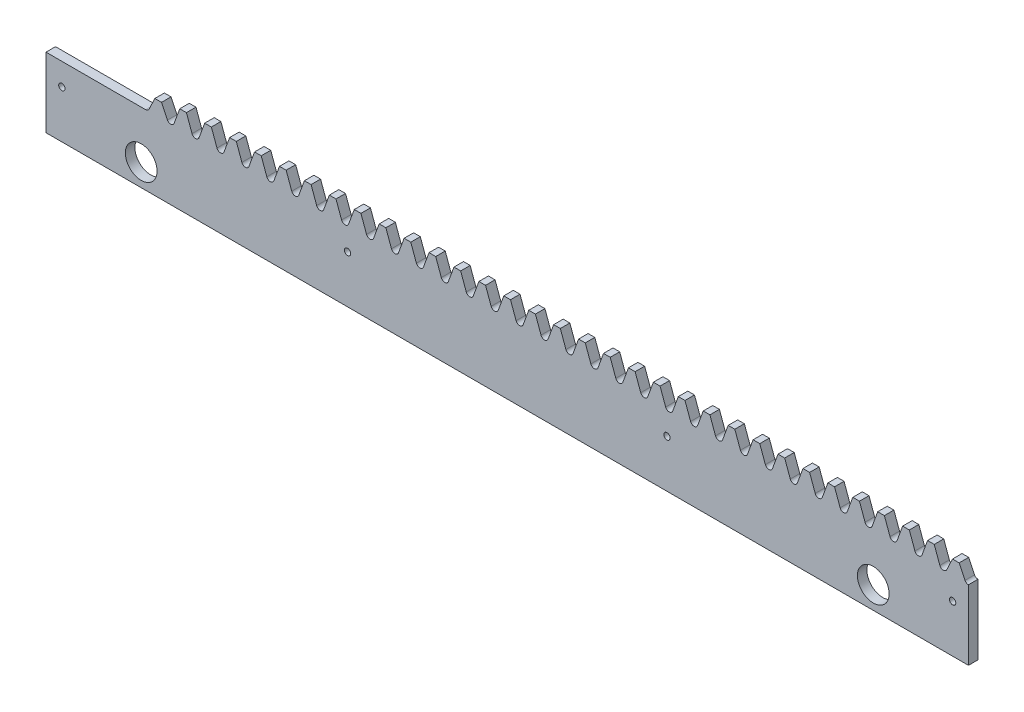
SolidWorks part; units mm, degrees
ref_plane "Plane1" through (0, 0, 0) normal (0, 0, 1) x (1, 0, 0)
ref_plane "Plane2" through (0, 0, 0) normal (0, 1, 0) x (1, 0, 0)
ref_plane "Plane3" through (0, 0, 0) normal (1, 0, 0) x (0, 0, -1)
sketch "Esquisse1" plane through (0, 0, 0) normal (0, 0, 1) x (1, 0, 0)
  line L0 (-11.781, 22) -> (19.635, 22)
  line L1 (23.5619, 29.1362) -> (23.5619, 19.2192) construction
  line L2 (-16.2297, 22) -> (24.6155, 22) construction
  line L3 (18.2522, 26.5) -> (283.3605, 26.5) construction
  line L4 (22.5084, 28.8854) -> (22.5084, 23.1798) construction
  line L5 (22.5084, 26.5) -> (20.6365, 22.5562)
  line L6 (24.6155, 26.5) -> (26.4874, 22.5562)
  line L8 (22.5084, 26.5) -> (24.6155, 26.5)
  line L10 (275.9429, 26.742) -> (275.9429, 19.9201) construction
  line L11 (273.8358, 26.742) -> (273.8358, 19.9201) construction
  line L12 (273.8358, 26.5) -> (272.0069, 22.6314)
  line L13 (275.9429, 26.5) -> (277.7718, 22.6314)
  line L14 (273.8358, 26.5) -> (275.9429, 26.5)
  line L20 (28.5976, 22.7763) -> (30.3624, 27.625)
  line L21 (30.3624, 27.625) -> (32.4695, 27.625)
  line L22 (34.2343, 22.7763) -> (32.4695, 27.625)
  line L23 (36.4515, 22.7763) -> (38.2163, 27.625)
  line L24 (38.2163, 27.625) -> (40.3235, 27.625)
  line L25 (42.0883, 22.7763) -> (40.3235, 27.625)
  line L26 (44.3055, 22.7763) -> (46.0703, 27.625)
  line L27 (46.0703, 27.625) -> (48.1775, 27.625)
  line L28 (49.9423, 22.7763) -> (48.1775, 27.625)
  line L29 (52.1595, 22.7763) -> (53.9243, 27.625)
  line L30 (53.9243, 27.625) -> (56.0314, 27.625)
  line L31 (57.7962, 22.7763) -> (56.0314, 27.625)
  line L32 (60.0135, 22.7763) -> (61.7783, 27.625)
  line L33 (61.7783, 27.625) -> (63.8854, 27.625)
  line L34 (65.6502, 22.7763) -> (63.8854, 27.625)
  line L35 (67.8675, 22.7763) -> (69.6323, 27.625)
  line L36 (69.6323, 27.625) -> (71.7394, 27.625)
  line L37 (73.5042, 22.7763) -> (71.7394, 27.625)
  line L38 (75.7215, 22.7763) -> (77.4862, 27.625)
  line L39 (77.4862, 27.625) -> (79.5934, 27.625)
  line L40 (81.3582, 22.7763) -> (79.5934, 27.625)
  line L41 (83.5754, 22.7763) -> (85.3402, 27.625)
  line L42 (85.3402, 27.625) -> (87.4474, 27.625)
  line L43 (89.2122, 22.7763) -> (87.4474, 27.625)
  line L44 (91.4294, 22.7763) -> (93.1942, 27.625)
  line L45 (93.1942, 27.625) -> (95.3013, 27.625)
  line L46 (97.0661, 22.7763) -> (95.3013, 27.625)
  line L47 (99.2834, 22.7763) -> (101.0482, 27.625)
  line L48 (101.0482, 27.625) -> (103.1553, 27.625)
  line L49 (104.9201, 22.7763) -> (103.1553, 27.625)
  line L50 (107.1374, 22.7763) -> (108.9022, 27.625)
  line L51 (108.9022, 27.625) -> (111.0093, 27.625)
  line L52 (112.7741, 22.7763) -> (111.0093, 27.625)
  line L53 (114.9914, 22.7763) -> (116.7562, 27.625)
  line L54 (116.7562, 27.625) -> (118.8633, 27.625)
  line L55 (120.6281, 22.7763) -> (118.8633, 27.625)
  line L56 (122.8453, 22.7763) -> (124.6101, 27.625)
  line L57 (124.6101, 27.625) -> (126.7173, 27.625)
  line L58 (128.4821, 22.7763) -> (126.7173, 27.625)
  line L59 (130.6993, 22.7763) -> (132.4641, 27.625)
  line L60 (132.4641, 27.625) -> (134.5713, 27.625)
  line L61 (136.3361, 22.7763) -> (134.5713, 27.625)
  line L62 (138.5533, 22.7763) -> (140.3181, 27.625)
  line L63 (140.3181, 27.625) -> (142.4252, 27.625)
  line L64 (144.19, 22.7763) -> (142.4252, 27.625)
  line L65 (146.4073, 22.7763) -> (148.1721, 27.625)
  line L66 (148.1721, 27.625) -> (150.2792, 27.625)
  line L67 (152.044, 22.7763) -> (150.2792, 27.625)
  line L68 (154.2613, 22.7763) -> (156.0261, 27.625)
  line L69 (156.0261, 27.625) -> (158.1332, 27.625)
  line L70 (159.898, 22.7763) -> (158.1332, 27.625)
  line L71 (162.1153, 22.7763) -> (163.88, 27.625)
  line L72 (163.88, 27.625) -> (165.9872, 27.625)
  line L73 (167.752, 22.7763) -> (165.9872, 27.625)
  line L74 (169.9692, 22.7763) -> (171.734, 27.625)
  line L75 (171.734, 27.625) -> (173.8412, 27.625)
  line L76 (175.606, 22.7763) -> (173.8412, 27.625)
  line L77 (177.8232, 22.7763) -> (179.588, 27.625)
  line L78 (179.588, 27.625) -> (181.6951, 27.625)
  line L79 (183.4599, 22.7763) -> (181.6951, 27.625)
  line L80 (185.6772, 22.7763) -> (187.442, 27.625)
  line L81 (187.442, 27.625) -> (189.5491, 27.625)
  line L82 (191.3139, 22.7763) -> (189.5491, 27.625)
  line L83 (193.5312, 22.7763) -> (195.296, 27.625)
  line L84 (195.296, 27.625) -> (197.4031, 27.625)
  line L85 (199.1679, 22.7763) -> (197.4031, 27.625)
  line L86 (201.3852, 22.7763) -> (203.15, 27.625)
  line L87 (203.15, 27.625) -> (205.2571, 27.625)
  line L88 (207.0219, 22.7763) -> (205.2571, 27.625)
  line L89 (209.2391, 22.7763) -> (211.0039, 27.625)
  line L90 (211.0039, 27.625) -> (213.1111, 27.625)
  line L91 (214.8759, 22.7763) -> (213.1111, 27.625)
  line L92 (217.0931, 22.7763) -> (218.8579, 27.625)
  line L93 (218.8579, 27.625) -> (220.9651, 27.625)
  line L94 (222.7298, 22.7763) -> (220.9651, 27.625)
  line L95 (224.9471, 22.7763) -> (226.7119, 27.625)
  line L96 (226.7119, 27.625) -> (228.819, 27.625)
  line L97 (230.5838, 22.7763) -> (228.819, 27.625)
  line L98 (232.8011, 22.7763) -> (234.5659, 27.625)
  line L99 (234.5659, 27.625) -> (236.673, 27.625)
  line L100 (238.4378, 22.7763) -> (236.673, 27.625)
  line L101 (240.6551, 22.7763) -> (242.4199, 27.625)
  line L102 (242.4199, 27.625) -> (244.527, 27.625)
  line L103 (246.2918, 22.7763) -> (244.527, 27.625)
  line L104 (248.509, 22.7763) -> (250.2738, 27.625)
  line L105 (250.2738, 27.625) -> (252.381, 27.625)
  line L106 (254.1458, 22.7763) -> (252.381, 27.625)
  line L107 (256.363, 22.7763) -> (258.1278, 27.625)
  line L108 (258.1278, 27.625) -> (260.235, 27.625)
  line L109 (261.9998, 22.7763) -> (260.235, 27.625)
  line L110 (264.217, 22.7763) -> (265.9818, 27.625)
  line L111 (265.9818, 27.625) -> (268.0889, 27.625)
  line L112 (269.8537, 22.7763) -> (268.0889, 27.625)
  line L114 (19.635, 37.0607) -> (19.635, -15.8181) construction
  line L115 (283.3605, 22) -> (228.0591, 22) construction
  line L118 (-11.781, 22) -> (-11.781, 0)
  line L121 (278.8759, 22.0015) -> (278.8759, 0)
  line L131 (278.8759, 0) -> (-11.781, 0)
  line L132 (133.5177, 28.2837) -> (133.5177, 9.5143) construction
  line L133 (130.5371, 22) -> (141.4123, 22) construction
  line L149 (273.8358, 27.625) -> (275.9429, 27.625) [skipped]
  line L150 (277.7077, 22.7763) -> (275.9429, 27.625) [skipped]
  line L151 (272.071, 22.7763) -> (273.8358, 27.625) [skipped]
  circle A0 centre (183.8759, 15) radius 1
  circle A1 centre (83.219, 15) radius 1
  arc A7 (19.635, 22) -> (20.6365, 22.5562) centre (19.635, 23.1798) ccw
  arc A8 (27.4889, 22) -> (26.4874, 22.5562) centre (27.4889, 23.1798) cw
  arc A9 (27.4889, 22) -> (28.5976, 22.7763) centre (27.4889, 23.1798) ccw
  arc A10 (35.3429, 22) -> (34.2343, 22.7763) centre (35.3429, 23.1798) cw
  arc A11 (35.3429, 22) -> (36.4515, 22.7763) centre (35.3429, 23.1798) ccw
  arc A12 (43.1969, 22) -> (42.0883, 22.7763) centre (43.1969, 23.1798) cw
  arc A13 (43.1969, 22) -> (44.3055, 22.7763) centre (43.1969, 23.1798) ccw
  arc A14 (51.0509, 22) -> (49.9423, 22.7763) centre (51.0509, 23.1798) cw
  arc A15 (51.0509, 22) -> (52.1595, 22.7763) centre (51.0509, 23.1798) ccw
  arc A16 (58.9049, 22) -> (57.7962, 22.7763) centre (58.9049, 23.1798) cw
  arc A17 (58.9049, 22) -> (60.0135, 22.7763) centre (58.9049, 23.1798) ccw
  arc A18 (66.7588, 22) -> (65.6502, 22.7763) centre (66.7588, 23.1798) cw
  arc A19 (66.7588, 22) -> (67.8675, 22.7763) centre (66.7588, 23.1798) ccw
  arc A20 (74.6128, 22) -> (73.5042, 22.7763) centre (74.6128, 23.1798) cw
  arc A21 (74.6128, 22) -> (75.7215, 22.7763) centre (74.6128, 23.1798) ccw
  arc A22 (82.4668, 22) -> (81.3582, 22.7763) centre (82.4668, 23.1798) cw
  arc A23 (82.4668, 22) -> (83.5754, 22.7763) centre (82.4668, 23.1798) ccw
  arc A24 (90.3208, 22) -> (89.2122, 22.7763) centre (90.3208, 23.1798) cw
  arc A25 (90.3208, 22) -> (91.4294, 22.7763) centre (90.3208, 23.1798) ccw
  arc A26 (98.1748, 22) -> (97.0661, 22.7763) centre (98.1748, 23.1798) cw
  arc A27 (98.1748, 22) -> (99.2834, 22.7763) centre (98.1748, 23.1798) ccw
  arc A28 (106.0288, 22) -> (104.9201, 22.7763) centre (106.0288, 23.1798) cw
  arc A29 (106.0288, 22) -> (107.1374, 22.7763) centre (106.0288, 23.1798) ccw
  arc A30 (113.8827, 22) -> (112.7741, 22.7763) centre (113.8827, 23.1798) cw
  arc A31 (113.8827, 22) -> (114.9914, 22.7763) centre (113.8827, 23.1798) ccw
  arc A32 (121.7367, 22) -> (120.6281, 22.7763) centre (121.7367, 23.1798) cw
  arc A33 (121.7367, 22) -> (122.8453, 22.7763) centre (121.7367, 23.1798) ccw
  arc A34 (129.5907, 22) -> (128.4821, 22.7763) centre (129.5907, 23.1798) cw
  arc A35 (129.5907, 22) -> (130.6993, 22.7763) centre (129.5907, 23.1798) ccw
  arc A36 (137.4447, 22) -> (136.3361, 22.7763) centre (137.4447, 23.1798) cw
  arc A37 (137.4447, 22) -> (138.5533, 22.7763) centre (137.4447, 23.1798) ccw
  arc A38 (145.2987, 22) -> (144.19, 22.7763) centre (145.2987, 23.1798) cw
  arc A39 (145.2987, 22) -> (146.4073, 22.7763) centre (145.2987, 23.1798) ccw
  arc A40 (153.1526, 22) -> (152.044, 22.7763) centre (153.1526, 23.1798) cw
  arc A41 (153.1526, 22) -> (154.2613, 22.7763) centre (153.1526, 23.1798) ccw
  arc A42 (161.0066, 22) -> (159.898, 22.7763) centre (161.0066, 23.1798) cw
  arc A43 (161.0066, 22) -> (162.1153, 22.7763) centre (161.0066, 23.1798) ccw
  arc A44 (168.8606, 22) -> (167.752, 22.7763) centre (168.8606, 23.1798) cw
  arc A45 (168.8606, 22) -> (169.9692, 22.7763) centre (168.8606, 23.1798) ccw
  arc A46 (176.7146, 22) -> (175.606, 22.7763) centre (176.7146, 23.1798) cw
  arc A47 (176.7146, 22) -> (177.8232, 22.7763) centre (176.7146, 23.1798) ccw
  arc A48 (184.5686, 22) -> (183.4599, 22.7763) centre (184.5686, 23.1798) cw
  arc A49 (184.5686, 22) -> (185.6772, 22.7763) centre (184.5686, 23.1798) ccw
  arc A50 (192.4226, 22) -> (191.3139, 22.7763) centre (192.4226, 23.1798) cw
  arc A51 (192.4226, 22) -> (193.5312, 22.7763) centre (192.4226, 23.1798) ccw
  arc A52 (200.2765, 22) -> (199.1679, 22.7763) centre (200.2765, 23.1798) cw
  arc A53 (200.2765, 22) -> (201.3852, 22.7763) centre (200.2765, 23.1798) ccw
  arc A54 (208.1305, 22) -> (207.0219, 22.7763) centre (208.1305, 23.1798) cw
  arc A55 (208.1305, 22) -> (209.2391, 22.7763) centre (208.1305, 23.1798) ccw
  arc A56 (215.9845, 22) -> (214.8759, 22.7763) centre (215.9845, 23.1798) cw
  arc A57 (215.9845, 22) -> (217.0931, 22.7763) centre (215.9845, 23.1798) ccw
  arc A58 (223.8385, 22) -> (222.7298, 22.7763) centre (223.8385, 23.1798) cw
  arc A59 (223.8385, 22) -> (224.9471, 22.7763) centre (223.8385, 23.1798) ccw
  arc A60 (231.6925, 22) -> (230.5838, 22.7763) centre (231.6925, 23.1798) cw
  arc A61 (231.6925, 22) -> (232.8011, 22.7763) centre (231.6925, 23.1798) ccw
  arc A62 (239.5464, 22) -> (238.4378, 22.7763) centre (239.5464, 23.1798) cw
  arc A63 (239.5464, 22) -> (240.6551, 22.7763) centre (239.5464, 23.1798) ccw
  arc A64 (247.4004, 22) -> (246.2918, 22.7763) centre (247.4004, 23.1798) cw
  arc A65 (247.4004, 22) -> (248.509, 22.7763) centre (247.4004, 23.1798) ccw
  arc A66 (255.2544, 22) -> (254.1458, 22.7763) centre (255.2544, 23.1798) cw
  arc A67 (255.2544, 22) -> (256.363, 22.7763) centre (255.2544, 23.1798) ccw
  arc A68 (263.1084, 22) -> (261.9998, 22.7763) centre (263.1084, 23.1798) cw
  arc A69 (263.1084, 22) -> (264.217, 22.7763) centre (263.1084, 23.1798) ccw
  arc A70 (270.9624, 22) -> (269.8537, 22.7763) centre (270.9624, 23.1798) cw
  arc A72 (270.9624, 22) -> (272.0069, 22.6314) centre (270.9624, 23.1798) ccw
  arc A79 (278.8759, 22.0015) -> (277.7718, 22.6314) centre (278.8163, 23.1798) cw
  circle A81 centre (-6.781, 15) radius 1
  circle A82 centre (273.8759, 15) radius 1
  point P9 (0, 0)
  dimension "D2" = 4.5
  dimension "D3" = 2
  dimension "D4" = 2
  dimension "D5" = 2
  dimension "D6" = 2
  dimension "D8" = 290.6568
  dimension "D9" = 90
  dimension "D10" = 5
  dimension "D11" = 90
  dimension "D7" = 5
  dimension "D12" = 100.6568
  dimension "D13" = 15
  dimension "D14" = 11.781
extrude "Extrusion1" add sketch "Esquisse1" along normal blind 3
sketch "Esquisse4" plane through (0, 0, 3) normal (0, 0, 1) x (1, 0, 0)
  line L0 (278.8759, 0) -> (-11.781, 0) construction
  line L1 (278.8759, 22.0015) -> (278.8759, 0) construction
  line L2 (-11.781, 22) -> (-11.781, 0) construction
  circle A0 centre (18.219, 7) radius 5
  circle A2 centre (248.8759, 7) radius 5
  dimension "D1" = 10
  dimension "D2" = 7
  dimension "D3" = 30
  dimension "D4" = 30
extrude "Enlèv. mat.-Extru.2" cut sketch "Esquisse4" against normal through all
